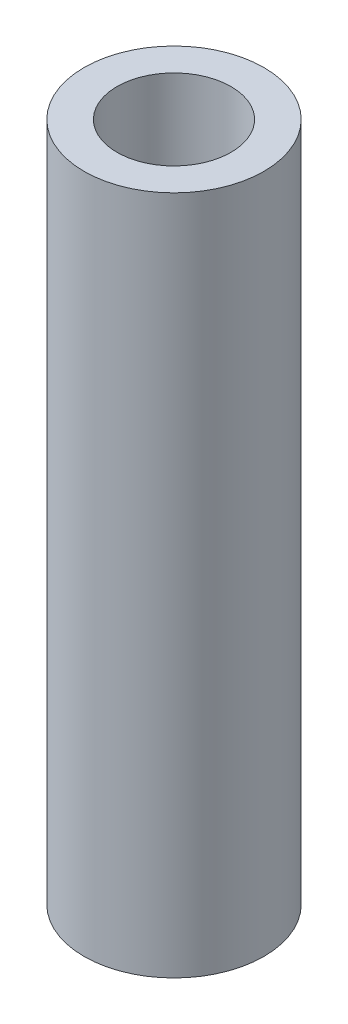
SolidWorks part; units mm, degrees
material "Cast Alloy Steel"
ref_plane "Front Plane" through (0, 0, 0) normal (0, 0, 1) x (1, 0, 0)
ref_plane "Top Plane" through (0, 0, 0) normal (0, 1, 0) x (1, 0, 0)
ref_plane "Right Plane" through (0, 0, 0) normal (1, 0, 0) x (0, 0, -1)
sketch "Sketch1" plane through (0, 0, 0) normal (0, 1, 0) x (1, 0, 0)
  circle A0 centre (0, 0) radius 4.7625
  circle A1 centre (0, 0) radius 3.019
  dimension "D1" = 9.525
extrude "Boss-Extrude1" add sketch "Sketch1" along normal mid plane 130
sketch "Sketch3" plane through (0, -65, 0) normal (0, -1, 0) x (1, 0, 0)
  circle A2 centre (0, 0) radius 4.7625
  circle A3 centre (0, 0) radius 4.7625
  dimension "D1" = 0
curve "Helix/Spiral1" pitch 2 height 320 turns 160
sketch "Sketch5" plane through (0, 0, 0) normal (1, 0, 0) x (0, 0, -1)
  line L0 (-3.019, -65) -> (3.019, -65) construction
  line L1 (15.559, 5) -> (-20.914, 5)
  line L2 (15.559, 5) -> (15.559, 86.3978)
  line L3 (15.559, 86.3978) -> (-20.914, 86.3978)
  line L4 (-20.914, 5) -> (-20.914, 86.3978)
  dimension "D1" = 70
extrude "Cut-Extrude2" cut sketch "Sketch5" against normal through all both and the other way through all
sketch "Sketch6" plane through (0, 0, 0) normal (1, 0, 0) x (0, 0, -1)
  line L0 (4.7625, 5) -> (-4.7625, 5) construction
  line L1 (-21.7865, -31) -> (15.4436, -31)
  line L2 (-21.7865, -31) -> (-21.7865, -75.0326)
  line L3 (-21.7865, -75.0326) -> (15.4436, -75.0326)
  line L4 (15.4436, -31) -> (15.4436, -75.0326)
  dimension "D1" = 36
extrude "Cut-Extrude3" cut sketch "Sketch6" against normal through all both and the other way through all
